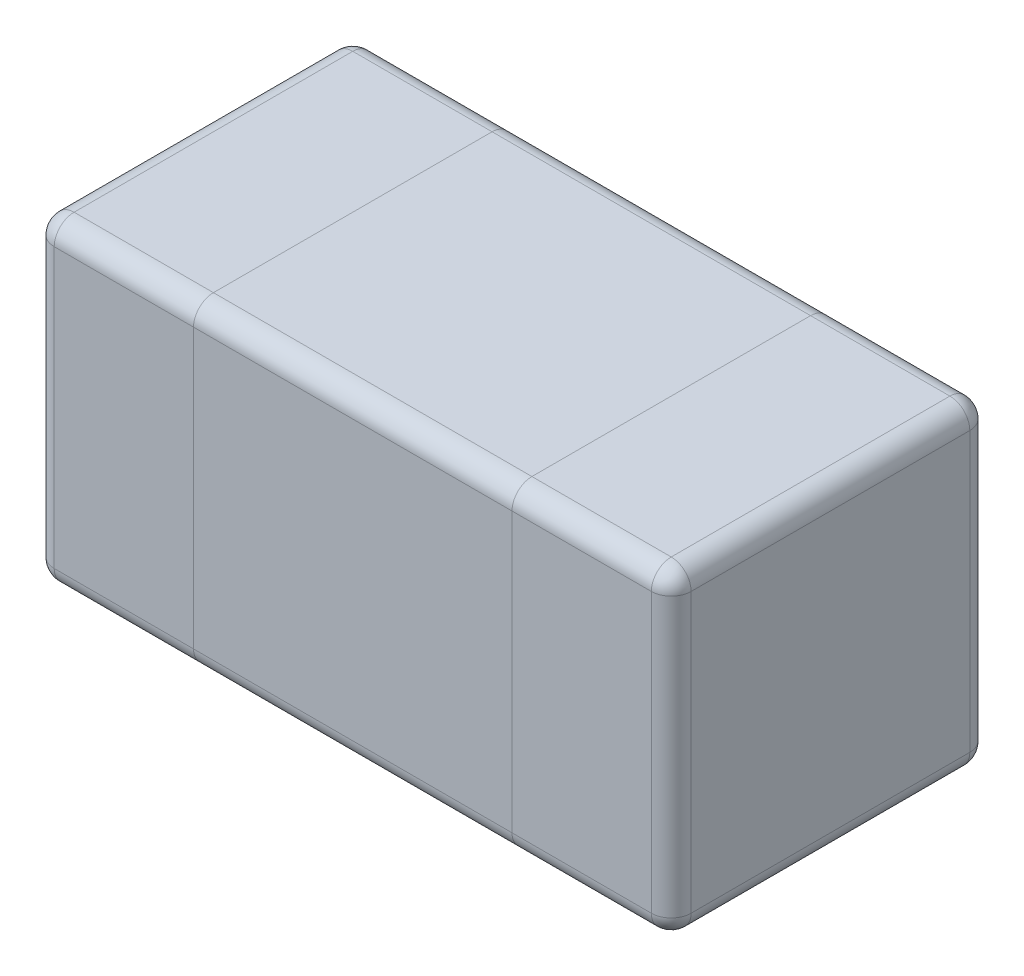
SolidWorks part; units mm, degrees
ref_plane "Front Plane" through (0, 0, 0) normal (0, 0, 1) x (1, 0, 0)
ref_plane "Top Plane" through (0, 0, 0) normal (0, 1, 0) x (1, 0, 0)
ref_plane "Right Plane" through (0, 0, 0) normal (1, 0, 0) x (0, 0, -1)
sketch "Sketch3" plane through (0, 0, 0) normal (0, 1, 0) x (1, 0, 0)
  line L1 (0, 0) -> (0.4, 0)
  line L2 (0, 0) -> (0, 0.8)
  line L3 (0, 0.8) -> (0.4, 0.8)
  line L4 (0.4, 0) -> (0.4, 0.8)
  line L5 (0.2, 0.8) -> (0.2, 0) construction
  line L6 (0, 0.4) -> (0.4, 0.4) construction
  line L7 (1.2, 0.8) -> (1.6, 0.8)
  line L8 (1.2, 0.8) -> (1.2, 0)
  line L9 (1.2, 0) -> (1.6, 0)
  line L10 (1.6, 0.8) -> (1.6, 0)
  line L11 (1.4, 0) -> (1.4, 0.8) construction
  line L12 (1.2, 0.4) -> (1.6, 0.4) construction
  point P100 (0.2, 0.4)
  point P138 (1.4, 0.4)
  dimension "D1" = 1.6
  dimension "D2" = 0.8
  dimension "D3" = 0.8
  dimension "D4" = 0.4
  dimension "D5" = 0.4
extrude "Boss-Extrude2" add sketch "Sketch3" along normal blind 0.8
sketch "Sketch4" plane through (0, 0, 0) normal (0, -1, 0) x (-1, 0, 0)
  line L1 (-0.4, 0.8) -> (-1.2, 0.8)
  line L2 (-0.4, 0.8) -> (-0.4, 0)
  line L3 (-0.4, 0) -> (-1.2, 0)
  line L4 (-1.2, 0.8) -> (-1.2, 0)
  line L5 (-0.8, 0) -> (-0.8, 0.8) construction
  line L6 (-0.4, 0.4) -> (-1.2, 0.4) construction
  point P164 (-0.8, 0.4)
extrude "Boss-Extrude3" add sketch "Sketch4" against normal blind 0.8 separate body
fillet "Fillet1" radius 0.05 8 edges at (0, 0.4, -0.8) (0, 0.8, -0.4) (0, 0.4, 0) (0, 0, -0.4) (0.2, 0.8, -0.8) (0.2, 0, -0.8) (0.2, 0, 0) (0.2, 0.8, 0)
fillet "Fillet2" radius 0.05 8 edges at (1.6, 0.4, 0) (1.6, 0.8, -0.4) (1.6, 0.4, -0.8) (1.6, 0, -0.4) (1.4, 0, 0) (1.4, 0, -0.8) (1.4, 0.8, 0) (1.4, 0.8, -0.8)
fillet "Fillet3" radius 0.05 4 edges at (0.8, 0, 0) (0.8, 0, -0.8) (0.8, 0.8, -0.8) (0.8, 0.8, 0)
